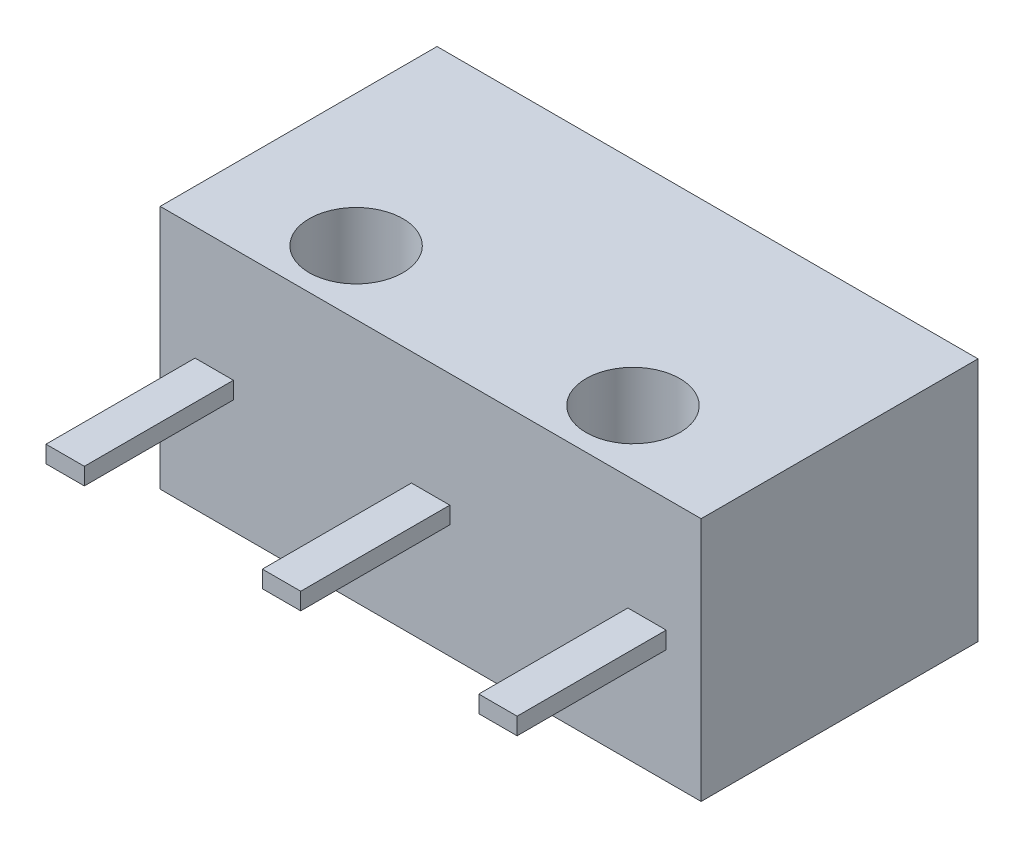
SolidWorks part; units mm, degrees
ref_plane "Front" through (0, 0, 0) normal (0, 0, 1) x (1, 0, 0)
ref_plane "Top" through (0, 0, 0) normal (0, 1, 0) x (1, 0, 0)
ref_plane "Right" through (0, 0, 0) normal (1, 0, 0) x (0, 0, -1)
sketch "Sketch1" plane through (0, 0, 0) normal (0, 1, 0) x (1, 0, 0)
  line L1 (0, 0) -> (12.7, 0)
  line L2 (0, 0) -> (0, 6.5)
  line L3 (0, 6.5) -> (12.7, 6.5)
  line L4 (12.7, 0) -> (12.7, 6.5)
  dimension "D1" = 12.7
  dimension "D2" = 6.5
extrude "Boss-Extrude1" add sketch "Sketch1" along normal blind 5.75
ref_plane "Plane1" through (0, 2.875, 0) normal (0, 1, 0) x (1, 0, 0)
sketch "Sketch5" plane through (0, 0, 0) normal (0, 1, 0) x (1, 0, 0)
  line L0 (-2.4393, 1.8082) -> (10.2607, 1.8082) construction
  dimension "D1" = 12.7
sketch "Sketch2" plane through (0, 5.75, 0) normal (0, 1, 0) x (1, 0, 0)
  line L0 (0, 0) -> (12.7, 0) construction
  line L1 (6.35, 0) -> (6.35, 1.5) construction
  line L2 (6.35, 1.5) -> (3.1, 1.5) construction
  line L3 (6.35, 1.5) -> (9.6, 1.5) construction
  circle A0 centre (3.1, 1.5) radius 1.1
  circle A1 centre (9.6, 1.5) radius 1.1
  dimension "D1" = 2.2
  dimension "D2" = 1.5
  dimension "D3" = 3.25
extrude "Cut-Extrude1" cut sketch "Sketch2" against normal through all
sketch "Sketch3" plane through (0, 2.875, 0) normal (0, 1, 0) x (1, 0, 0)
  line L0 (6.35, 0) -> (6.35, -3.5) construction
  line L1 (0, 0) -> (12.7, 0) construction
  line L2 (5.9, -3.5) -> (6.8, -3.5)
  line L3 (6.8, -3.5) -> (6.8, 0)
  line L4 (5.9, -3.5) -> (5.9, 0)
  line L5 (11.43, 0) -> (11.43, -3.5) construction
  line L6 (11.88, 0) -> (11.88, -3.5)
  line L7 (11.88, -3.5) -> (11.43, -3.5)
  line L8 (11.43, -3.5) -> (10.98, -3.5)
  line L9 (10.98, -3.5) -> (10.98, 0)
  line L10 (0.82, 0) -> (1.72, 0)
  line L12 (1.72, -3.5) -> (1.72, 0)
  line L14 (5.9, 0) -> (6.8, 0)
  line L15 (11.88, 0) -> (10.98, 0)
  line L16 (1.27, -3.5) -> (1.72, -3.5)
  line L17 (0.82, -3.5) -> (1.27, -3.5)
  line L18 (0.82, 0) -> (0.82, -3.5)
  dimension "D1" = 3.5
  dimension "D2" = 0.9
  dimension "D3" = 5.08
  dimension "D4" = 0.9
extrude "Boss-Extrude2" add sketch "Sketch3" along normal blind 0.2 and the other way blind 0.2
sketch "Sketch4" plane through (0, 2.875, 0) normal (0, 1, 0) x (1, 0, 0)
  line L0 (3.8, 6.5) -> (5, 6.5)
  line L1 (12.7, 6.5) -> (0, 6.5) construction
  arc A0 (3.8, 6.5) -> (5, 6.5) centre (4.4, 6.5) cw
  circle A1 centre (9.6, 1.5) radius 1.1 construction
  dimension "D1" = 5.2
  dimension "D2" = 1.2
extrude "Boss-Extrude3" add sketch "Sketch4" along normal blind 1.45 and the other way blind 1.45
equation "\"D4@Sketch3\"=\"D2@Sketch3\""
